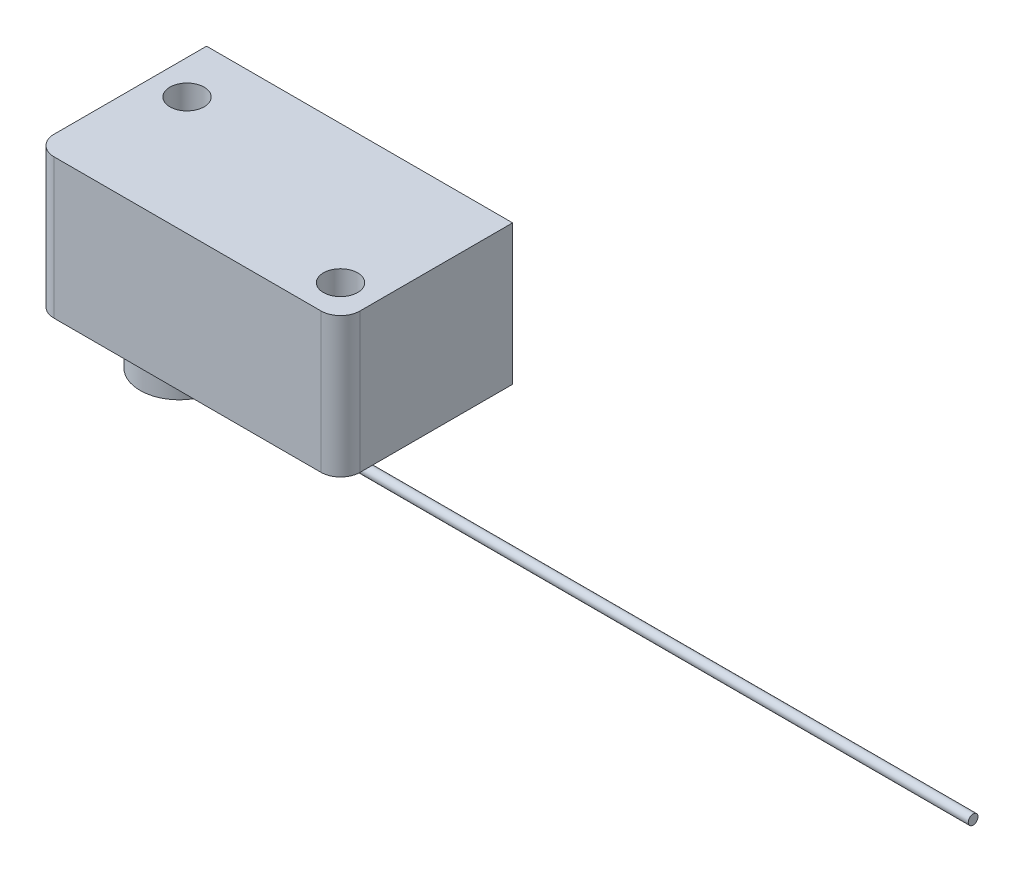
SolidWorks part; units mm, degrees
ref_plane "Front" through (0, 0, 0) normal (0, 0, 1) x (1, 0, 0)
ref_plane "Top" through (0, 0, 0) normal (0, 1, 0) x (1, 0, 0)
ref_plane "Right" through (0, 0, 0) normal (1, 0, 0) x (0, 0, -1)
sketch "草圖1" plane through (0, 0, 0) normal (0, 1, 0) x (1, 0, 0)
  line L1 (2, 0) -> (29.3, 0)
  line L2 (0, 2) -> (0, 17.6)
  line L3 (0, 17.6) -> (31.3, 17.6)
  line L4 (31.3, 2) -> (31.3, 17.6)
  arc A0 (2, 0) -> (0, 2) centre (2, 2) cw
  arc A1 (29.3, 0) -> (31.3, 2) centre (29.3, 2) ccw
  point P7 (0, 0)
  point P10 (31.3, 0)
  dimension "D3" = 2
  dimension "D1" = 31.3
  dimension "D2" = 17.6
extrude "填料-伸長1" add sketch "草圖1" along normal blind 14.3
sketch "草圖2" plane through (0, 14.3, 0) normal (0, 1, 0) x (1, 0, 0)
  line L0 (31.3, 2) -> (31.3, 17.6) construction
  line L1 (2, 0) -> (29.3, 0) construction
  line L2 (0, 17.6) -> (0, 2) construction
  circle A0 centre (27.8, 3.5) radius 1.75
  circle A1 centre (3.5, 12.1) radius 1.75
  dimension "D1" = 3.5
  dimension "D2" = 3.5
  dimension "D3" = 3.5
  dimension "D4" = 12.1
  dimension "D5" = 3.5
  dimension "D6" = 3.5
extrude "除料-伸長1" cut sketch "草圖2" against normal through all
sketch "草圖3" plane through (0, 0, 0) normal (0, -1, 0) x (1, 0, 0)
  line L0 (2, 0) -> (29.3, 0) construction
  line L1 (0, -17.6) -> (0, -2) construction
  circle A0 centre (8.8, -6) radius 4
  dimension "D1" = 6
  dimension "D2" = 8
  dimension "D3" = 8.8
extrude "填料-伸長2" add sketch "草圖3" along normal blind 4
sketch "草圖4" plane through (0, 0, 0) normal (-1, 0, 0) x (0, 0, 1)
  line L0 (-6, -4) -> (-6, -3.4) construction
  line L1 (-10, -4) -> (-2, -4) construction
  circle A0 centre (-6, -3.4) radius 0.5
  dimension "D1" = 1
  dimension "D2" = 0.6
extrude "填料-伸長3" add sketch "草圖4" against normal blind 80 from offset 10
